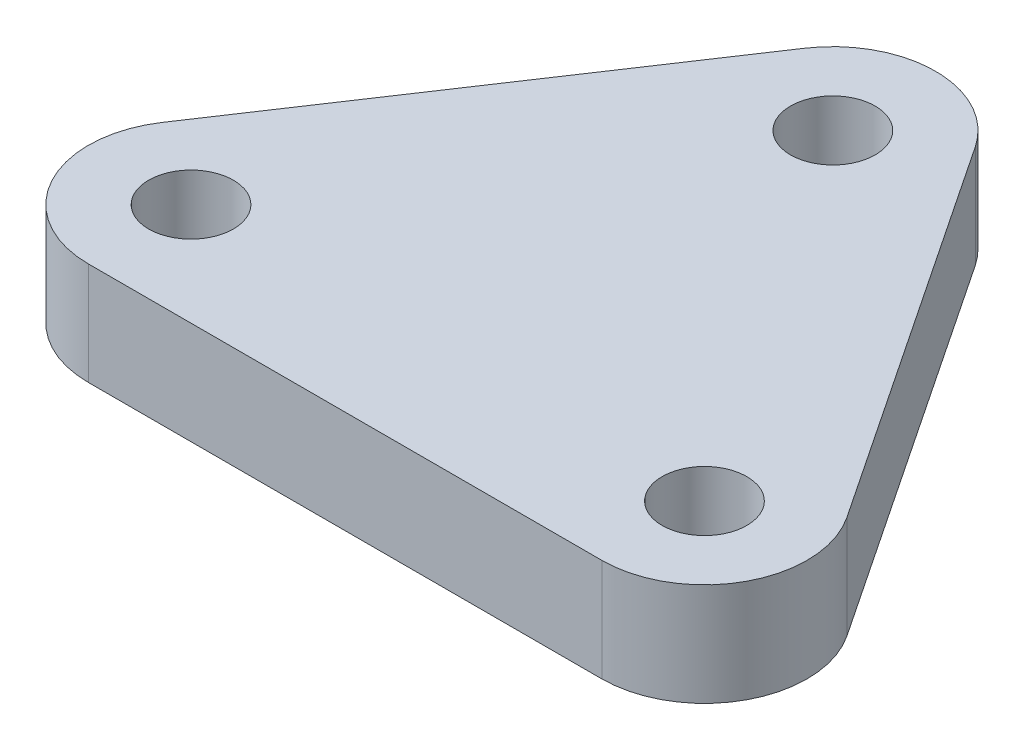
SolidWorks part; units mm, degrees
material "6061 合金"
ref_plane "前视基准面" through (0, 0, 0) normal (0, 0, 1) x (1, 0, 0)
ref_plane "上视基准面" through (0, 0, 0) normal (0, 1, 0) x (1, 0, 0)
ref_plane "右视基准面" through (0, 0, 0) normal (1, 0, 0) x (0, 0, -1)
sketch "草图1" plane through (0, 0, 0) normal (0, 1, 0) x (1, 0, 0)
  line L0 (-10, 0) -> (10, 0) construction
  line L1 (0, 0) -> (0, 15) construction
  line L2 (-3.3282, 17.2188) -> (-13.3282, 2.2188)
  line L3 (-10, -4) -> (10, -4)
  line L4 (13.3282, 2.2188) -> (3.3282, 17.2188)
  arc A0 (10, -4) -> (13.3282, 2.2188) centre (10, 0) ccw
  arc A1 (-13.3282, 2.2188) -> (-10, -4) centre (-10, 0) ccw
  arc A2 (-3.3282, 17.2188) -> (3.3282, 17.2188) centre (0, 15) cw
  dimension "D3" = 4
  dimension "D1" = 20
  dimension "D2" = 15
extrude "凸台-拉伸1" add sketch "草图1" along normal blind 4
hole_wizard "M4 螺纹孔1" positions "草图2" profile "草图3" tap size "M4" standard "GB" end condition through all
sketch "草图2" plane through (0, 4, 0) normal (0, 1, 0) x (1, 0, 0)
  point P0 (0, 15)
  point P3 (-10, 0)
  point P6 (10, 0)
sketch "草图3" plane through (0, 4, -15) normal (1, 0, 0) x (0, 0, 1)
  line L0 (0, 0) -> (0, 4)
  line L1 (0, 4) -> (1.65, 4)
  line L2 (1.65, 4) -> (1.65, 0)
  line L5 (1.65, 0) -> (0, 0)
  line L11 (0, -6.35) -> (0, 107.95) construction
  dimension "通孔螺纹孔钻头直径" = 3.3
  dimension "通孔螺纹孔钻头深度" = 4
cosmetic thread "孔螺蚊线1" parameters "D2"=4
cosmetic thread "孔螺蚊线2" parameters "D2"=4
cosmetic thread "孔螺蚊线3" parameters "D2"=4
